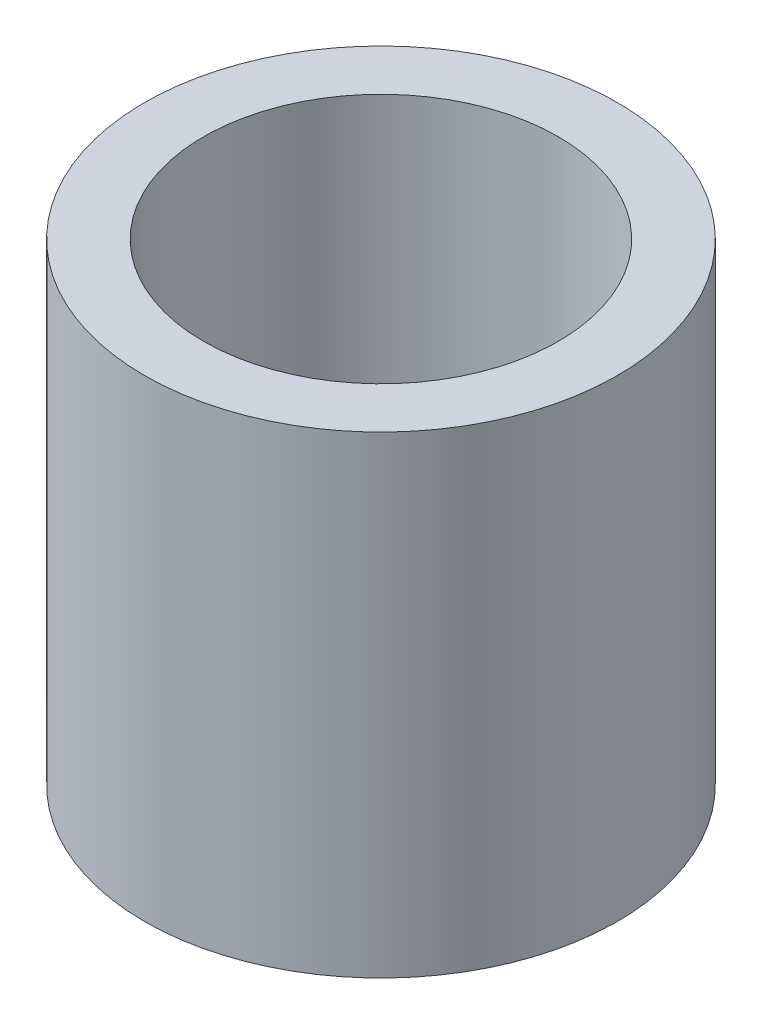
SolidWorks part; units mm, degrees
ref_plane "Front Plane" through (0, 0, 0) normal (0, 0, 1) x (1, 0, 0)
ref_plane "Top Plane" through (0, 0, 0) normal (0, 1, 0) x (1, 0, 0)
ref_plane "Right Plane" through (0, 0, 0) normal (1, 0, 0) x (0, 0, -1)
sketch "Sketch1" plane through (0, 0, 0) normal (0, 1, 0) x (1, 0, 0)
  circle A0 centre (0, 0) radius 2.3813
  circle A1 centre (0, 0) radius 3.175
  dimension "D1" = 4.7625
  dimension "D2" = 6.35
extrude "Boss-Extrude1" add sketch "Sketch1" along normal blind 6.35
